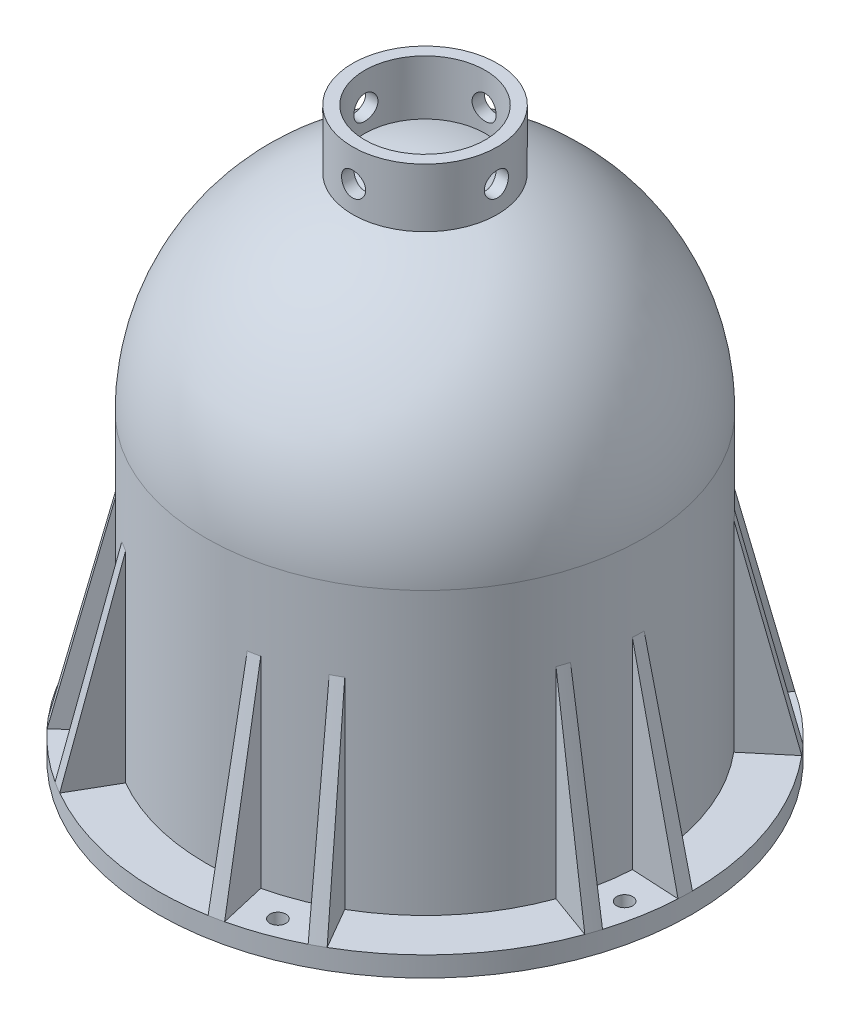
SolidWorks part; units mm, degrees
material "Polyester Resin"
ref_plane "Front Plane" through (0, 0, 0) normal (0, 0, 1) x (1, 0, 0)
ref_plane "Top Plane" through (0, 0, 0) normal (0, 1, 0) x (1, 0, 0)
ref_plane "Right Plane" through (0, 0, 0) normal (1, 0, 0) x (0, 0, -1)
ref_axis "Axis1" through (0, 98.5378, 0) along (0, -1, 0)
sketch "Sketch1" plane through (0, 0, 0) normal (0, 0, 1) x (1, 0, 0)
  line L0 (0, 0) -> (50.5, 0) construction
  line L1 (54.5, 0) -> (54.5, -70)
  line L2 (50.5, -70) -> (54.5, -70) construction
  line L3 (0, 98.5378) -> (0, -108.4725) construction
  line L4 (50.5, 0) -> (54.5, 0) construction
  line L6 (0, 54.5) -> (0, 50.5)
  line L7 (50.5, 0) -> (50.5, -70)
  line L8 (50.5, -70) -> (50.5, -75)
  line L11 (54.5, -70) -> (66.5, -70)
  line L12 (66.5, -70) -> (66.5, -75)
  line L15 (50.5, -75) -> (66.5, -75)
  arc A0 (54.5, 0) -> (0, 54.5) centre (0, 0) ccw
  arc A1 (50.5, 0) -> (0, 50.5) centre (0, 0) ccw
  dimension "D1" = 50.5
  dimension "D3" = 5
  dimension "D4" = 4
  dimension "D6" = 70
  dimension "D7" = 12
revolve "Revolve1" add sketch "Sketch1" angle 360 about axis through (0, 98.5378, 0) along (0, -1, 0)
sketch "Sketch2" plane through (0, 0, 0) normal (0, 0, 1) x (1, 0, 0)
  line L0 (54.5, -20) -> (66.5, -70)
  line L1 (66.5, -70) -> (54.5, -70)
  line L2 (54.5, -70) -> (54.5, -20)
  line L3 (54.5, -70) -> (54.5, 0) construction
  dimension "D1" = 50
revolve "Revolve2" add sketch "Sketch2" angle 3 about axis through (0, 98.5378, 0) along (0, -1, 0)
pattern_circular "CirPattern1" count 2 every 17 about axis through (0, 0, 0) along (0, 1, 0) of "Revolve2"
sketch "Sketch3" plane through (0, -70, 0) normal (0, 1, 0) x (1, 0, 0)
  line L0 (52.1186, -15.9343) -> (54.4253, -2.8523) construction
  line L1 (54.4253, -2.8523) -> (61.5769, -3.2271) construction
  line L2 (54.4253, -2.8523) -> (66.4089, -3.4803) construction
  line L3 (61.5769, -3.2271) -> (58.9671, -18.028) construction
  line L4 (52.1186, -15.9343) -> (63.5943, -19.4427) construction
  line L5 (58.9671, -18.028) -> (52.1186, -15.9343) construction
  line L6 (53.272, -9.3933) -> (60.272, -10.6276) construction
  circle A0 centre (60.272, -10.6276) radius 2
  circle A1 centre (60.272, -10.6276) radius 6 construction
  dimension "D2" = 4
  dimension "D3" = 12
  dimension "D1" = 7
extrude "Cut-Extrude1" cut sketch "Sketch3" against normal up to next contours A0
pattern_circular "CirPattern2" count 6 over 360 about axis through (0, 0, 0) along (0, 1, 0) of "Cut-Extrude1", "Revolve2", "CirPattern1"
sketch "Sketch4" plane through (0, 0, 0) normal (0, 1, 0) x (1, 0, 0)
  line L0 (0, 0) -> (0, -49.5)
  line L1 (-35.7089, -35.7089) -> (35.7089, -35.7089) construction
  line L2 (-35.7089, -35.7089) -> (-35.7089, 35.7089) construction
  line L3 (-35.7089, 35.7089) -> (35.7089, 35.7089) construction
  line L4 (35.7089, -35.7089) -> (35.7089, 35.7089) construction
  line L5 (-31.552, -33.7601) -> (-31.552, -39.4299)
  line L6 (-33.7601, -31.552) -> (-39.4299, -31.552)
  line L7 (0, -49.5) -> (0, -50.5)
  line L8 (-28.552, -33.7601) -> (-28.552, -41.6537)
  line L9 (-30.052, -30.052) -> (0, 0) construction
  line L13 (-33.7601, -28.552) -> (-41.6537, -28.552)
  line L18 (-39.4299, -31.552) -> (-39.4299, -28.552) construction
  line L20 (-31.552, -39.4299) -> (-28.552, -39.4299) construction
  circle A0 centre (0, 0) radius 50.5 construction
  circle A1 centre (-30.052, -30.052) radius 1.25
  arc A2 (-28.552, -33.7601) -> (-33.7601, -28.552) centre (-30.052, -30.052) ccw
  circle A3 centre (0, 0) radius 50.5 construction
  arc A4 (-33.7601, -31.552) -> (-31.552, -33.7601) centre (-30.052, -30.052) ccw
  circle A6 centre (0, 0) radius 49.5 construction
  arc A7 (-41.6537, -28.552) -> (-39.4299, -31.552) centre (0, 0) cw construction
  arc A8 (-31.552, -39.4299) -> (-28.552, -41.6537) centre (0, 0) ccw
  arc A9 (-41.6537, -28.552) -> (-39.4299, -31.552) centre (0, 0) ccw
  point P7 (-30.052, -39.4299)
  point P8 (-39.4299, -30.052)
  dimension "D2" = 2.5
  dimension "D1" = 8
  dimension "D3" = 3
  dimension "D4" = 1
  dimension "D5" = 8
  dimension "D6" = 42.5
extrude "Boss-Extrude1" add sketch "Sketch4" along normal up to surface (24.3984 mm away) contours L13 A9 L6 A4 L5 A8 L8 A2 A1
pattern_circular "CirPattern3" count 4 over 360 about axis through (0, 0, 0) along (0, 1, 0) of "Boss-Extrude1"
ref_plane "Plane1" through (0, 66, 0) normal (0, 1, 0) x (1, 0, 0)
sketch "Sketch5" plane through (0, 66, 0) normal (0, 1, 0) x (1, 0, 0)
  line L0 (0, 0) -> (0, 15) construction
  line L1 (0, 15) -> (0, 18) construction
  circle A0 centre (0, 0) radius 15
  circle A1 centre (0, 0) radius 18
  dimension "D2" = 30
  dimension "D1" = 3
extrude "Boss-Extrude2" add sketch "Sketch5" against normal up to surface (13.6049 mm away)
sketch "Sketch6" plane through (0, 0, 0) normal (0, 0, 1) x (1, 0, 0)
  line L0 (0, 61) -> (0, 66) construction
  line L1 (18, 66) -> (-18, 66) construction
  circle A0 centre (0, 58) radius 3
  dimension "D2" = 6
  dimension "D1" = 5
extrude "Cut-Extrude2" cut sketch "Sketch6" against normal through all and the other way through all
pattern_circular "CirPattern4" count 2 every 90 about axis through (0, 98.5378, 0) along (0, -1, 0) of "Cut-Extrude2"
